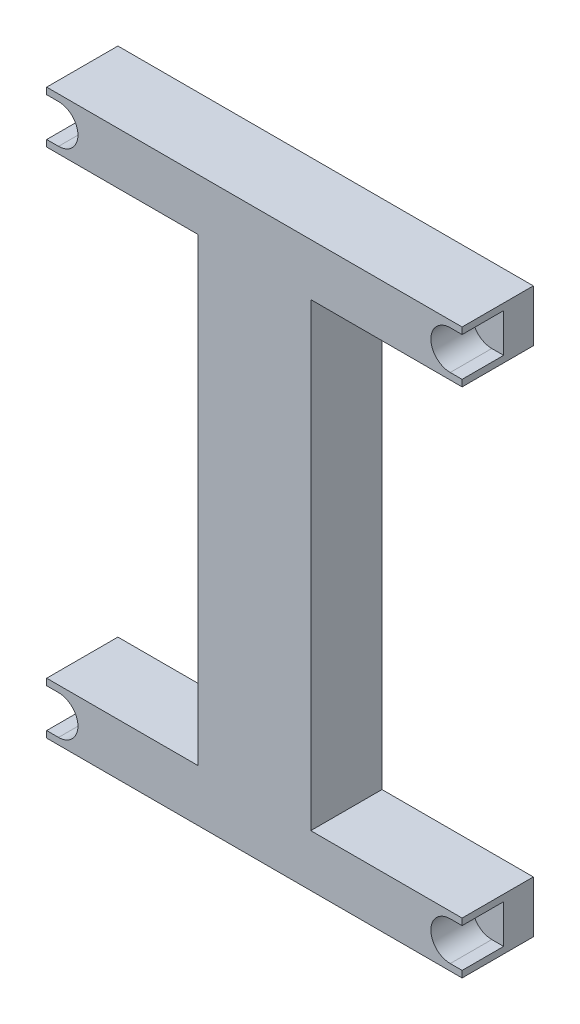
SolidWorks part; units mm, degrees
ref_plane "Front Plane" through (0, 0, 0) normal (0, 0, 1) x (1, 0, 0)
ref_plane "Top Plane" through (0, 0, 0) normal (0, 1, 0) x (1, 0, 0)
ref_plane "Right Plane" through (0, 0, 0) normal (1, 0, 0) x (0, 0, -1)
sketch "Sketch1" plane through (0, 0, 0) normal (0, 0, 1) x (1, 0, 0)
  line L0 (0, -125.3688) -> (0, 127.303) construction
  line L1 (-70, 95) -> (70, 95)
  line L2 (-70, 95) -> (-70, -95)
  line L3 (-70, -95) -> (70, -95)
  line L4 (70, 95) -> (70, -95)
  line L5 (-70, 95) -> (70, -95) construction
  line L6 (-70, -95) -> (70, 95) construction
  line L7 (-35, 95) -> (-35, -95)
  line L8 (35, 95) -> (35, -95)
  line L9 (-35, 77.5) -> (-70, 77.5)
  line L10 (35, 77.5) -> (70, 77.5)
  line L11 (-35, -77.5) -> (-70, -77.5)
  line L12 (35, -77.5) -> (70, -77.5)
  point P0 (0, 0)
  point P8 (0, 95)
  point P9 (-35, 95)
  point P10 (-35, 95)
  point P15 (-35, 52.7509)
  point P16 (35, 47.5)
  point P17 (-35, 77.5)
  point P21 (-35, 95)
  point P23 (-35, -77.5)
  dimension "D1" = 190
  dimension "D2" = 140
  dimension "D3" = 35
  dimension "D4" = 35
  dimension "D5" = 17.5
  dimension "D6" = 17.5
extrude "Boss-Extrude1" add sketch "Sketch1" along normal blind 24 contours L11 L7 L9 L2 | L9 L7 L1 L2 | L8 L1 L7 L3 | L8 L10 L4 L1 | L8 L12 L4 L10 | L12 L8 L3 L4 | L7 L11 L2 L3
sketch "Sketch2" plane through (0, 0, 24) normal (0, 0, 1) x (1, 0, 0)
  line L0 (0, 95) -> (0, -95)
  line L1 (-70, 95) -> (70, 95) construction
  line L2 (-70, -95) -> (70, -95) construction
  line L3 (-70, 0) -> (0, 0)
  line L4 (-70, 95) -> (-70, -95) construction
  line L5 (0, 0) -> (70, 0)
  line L6 (70, 95) -> (70, -95) construction
  line L7 (-70, 95) -> (-70, 77.5)
  line L8 (-70, 77.5) -> (0, 77.5)
  line L9 (0, 77.5) -> (0, -77.5)
  line L10 (0, -77.5) -> (-70, -77.5)
  line L11 (-70, -77.5) -> (-70, -95)
  line L12 (-70, -95) -> (0, -95)
  line L13 (-70, 95) -> (0, 95)
  line L14 (-19, 77.5) -> (-19, -77.5)
  line L15 (19, 77.5) -> (19, -77.5)
  line L16 (0, 77.5) -> (35, 77.5)
  line L17 (70, 77.5) -> (70, 95)
  line L18 (70, 95) -> (0, 95)
  line L19 (35, 77.5) -> (70, 77.5)
  line L20 (0, -77.5) -> (35, -77.5)
  line L21 (35, -77.5) -> (70, -77.5)
  line L22 (70, -77.5) -> (70, -95)
  line L23 (70, -95) -> (0, -95)
  point P16 (-35, 77.5)
  dimension "D1" = 19
extrude "Cut-Extrude1" cut sketch "Sketch2" against normal blind 24
sketch "Sketch3" plane through (0, 0, 24) normal (0, 0, 1) x (1, 0, 0)
  line L0 (70, -77.5) -> (70, -95) construction
  line L1 (70, -86.25) -> (66, -86.25) construction
  line L2 (70, -92.7812) -> (66, -92.7812)
  line L3 (70, -79.7188) -> (66, -79.7188)
  line L4 (0, -118.6563) -> (0, 157.1609) construction
  line L5 (-141.1981, 0) -> (141.3942, 0) construction
  line L6 (70, 86.25) -> (66, 86.25) construction
  line L7 (70, 92.7812) -> (66, 92.7812)
  line L8 (70, 79.7188) -> (66, 79.7188)
  line L9 (-70, 86.25) -> (-66, 86.25) construction
  line L10 (-70, 92.7812) -> (-66, 92.7812)
  line L11 (-70, 79.7188) -> (-66, 79.7188)
  line L12 (-70, -86.25) -> (-66, -86.25) construction
  line L13 (-70, -92.7812) -> (-66, -92.7812)
  line L14 (-70, -79.7188) -> (-66, -79.7188)
  arc A0 (70, -92.7812) -> (70, -79.7188) centre (70, -86.25) ccw
  arc A1 (66, -79.7188) -> (66, -92.7812) centre (66, -86.25) ccw
  arc A2 (70, 92.7812) -> (70, 79.7188) centre (70, 86.25) cw
  arc A3 (66, 79.7188) -> (66, 92.7812) centre (66, 86.25) cw
  arc A4 (-70, 92.7812) -> (-70, 79.7188) centre (-70, 86.25) ccw
  arc A5 (-66, 79.7188) -> (-66, 92.7812) centre (-66, 86.25) ccw
  arc A6 (-70, -92.7812) -> (-70, -79.7188) centre (-70, -86.25) cw
  arc A7 (-66, -79.7188) -> (-66, -92.7812) centre (-66, -86.25) cw
  point P4 (68, -86.25)
  point P16 (68, 86.25)
  point P23 (-68, 86.25)
  point P28 (0, 0)
  point P31 (-68, -86.25)
  dimension "D1" = 4
extrude "Cut-Extrude2" cut sketch "Sketch3" against normal blind 14
